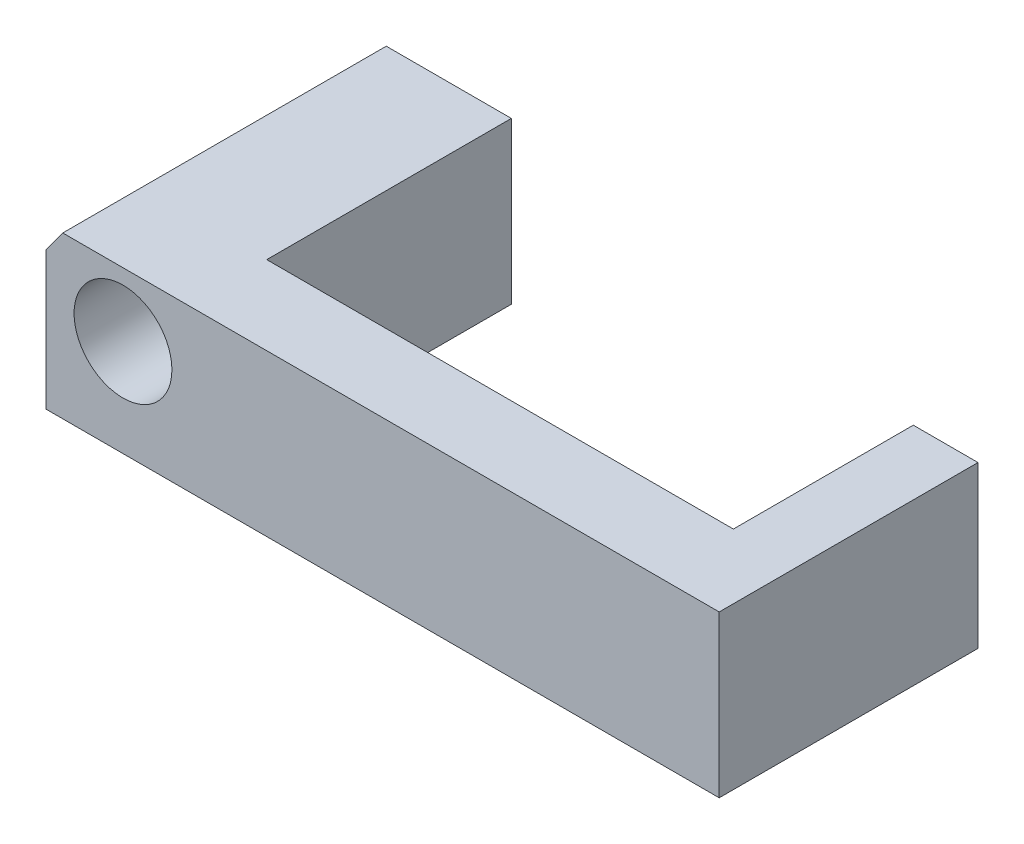
SolidWorks part; units mm, degrees
ref_plane "Front Plane" through (0, 0, 0) normal (0, 0, 1) x (1, 0, 0)
ref_plane "Top Plane" through (0, 0, 0) normal (0, 1, 0) x (1, 0, 0)
ref_plane "Right Plane" through (0, 0, 0) normal (1, 0, 0) x (0, 0, -1)
sketch "Sketch1" plane through (0, 0, 0) normal (0, 0, 1) x (1, 0, 0)
  line L0 (-89.45, -55.2) -> (-94.05, -55.2) construction
  line L1 (-96.8112, -63.5) -> (-89.85, -63.5)
  line L2 (-96.8112, -63.5) -> (-96.8112, -56.7311)
  line L3 (-95.9886, -55.6) -> (-89.85, -55.6)
  line L4 (-89.85, -63.5) -> (-89.85, -55.6)
  line L5 (-89.45, -59.1) -> (-89.45, -55.2) construction
  line L6 (-95.9886, -55.6) -> (-96.8112, -56.7311)
  line L7 (-98.8177, -59.49) -> (-89.1541, -46.2024) construction
  line L8 (-73.5606, -63.5) -> (-96.25, -63.5) construction
  dimension "D1" = 0.4
  dimension "D2" = 0.4
extrude "Boss-Extrude1" add sketch "Sketch1" along normal blind 15.875
sketch "Sketch2" plane through (-89.85, 0, 0) normal (1, 0, 0) x (0, 0, -1)
  line L0 (-15.875, -55.6) -> (0, -55.6) construction
  line L1 (-15.875, -63.5) -> (-12.0042, -63.5)
  line L2 (-15.875, -63.5) -> (-15.875, -55.6)
  line L3 (-15.875, -55.6) -> (-12.0042, -55.6)
  line L4 (-12.0042, -63.5) -> (-12.0042, -55.6)
  dimension "D1" = 0.4
extrude "Boss-Extrude2" add sketch "Sketch2" along normal up to surface (22.9 mm away)
sketch "Sketch3" plane through (0, 0, 15.875) normal (0, 0, 1) x (1, 0, 0)
  line L1 (-66.95, -63.5) -> (-63.775, -63.5)
  line L2 (-66.95, -63.5) -> (-66.95, -55.6)
  line L3 (-66.95, -55.6) -> (-63.775, -55.6)
  line L4 (-63.775, -63.5) -> (-63.775, -55.6)
  dimension "D1" = 3.175
extrude "Boss-Extrude3" add sketch "Sketch3" against normal blind 12.7
sketch "Sketch4" plane through (0, 0, 15.875) normal (0, 0, 1) x (1, 0, 0)
  circle A0 centre (-93.0328, -58.7375) radius 2.4003
  dimension "D1" = 4.8006
extrude "Cut-Extrude1" cut sketch "Sketch4" against normal through all
